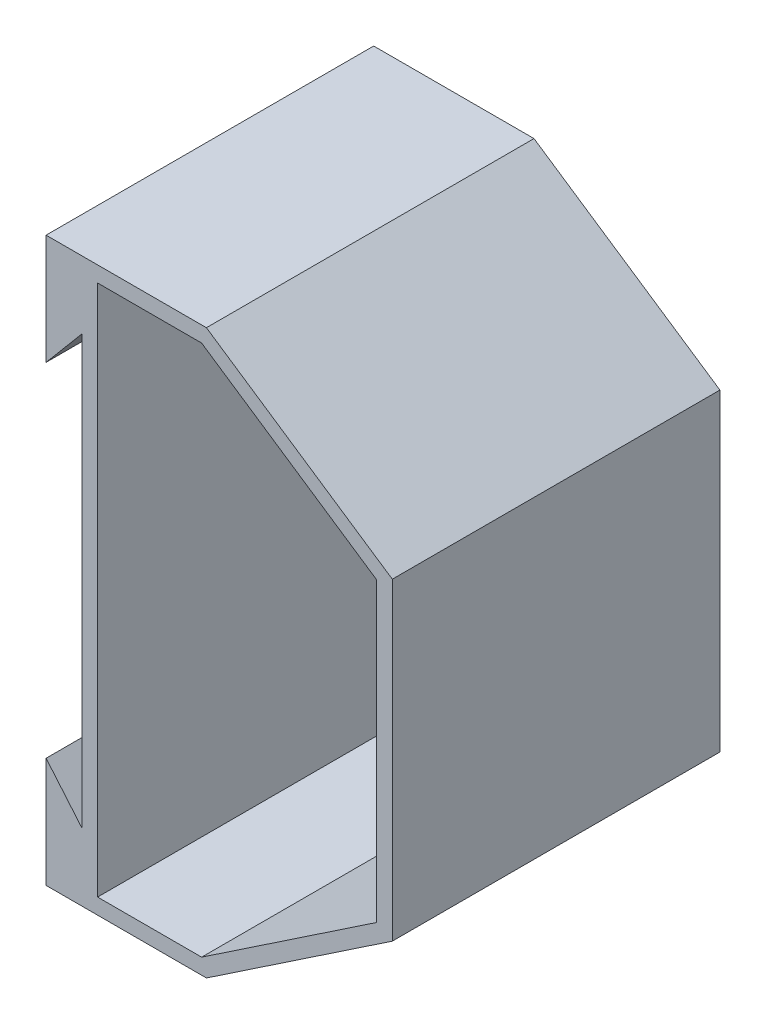
SolidWorks part; units mm, degrees
ref_plane "Alzado" through (0, 0, 0) normal (0, 0, 1) x (1, 0, 0)
ref_plane "Planta" through (0, 0, 0) normal (0, 1, 0) x (1, 0, 0)
ref_plane "Vista lateral" through (0, 0, 0) normal (1, 0, 0) x (0, 0, -1)
sketch "Croquis1" plane through (0, 0, 0) normal (0, 0, 1) x (1, 0, 0)
  line L0 (0, 0) -> (154.6177, 0) construction
  line L4 (154.6177, 70) -> (71.6, 125.75)
  line L5 (71.6, 125.75) -> (0, 125.75)
  line L6 (0, 125.75) -> (0, 76.55)
  line L7 (0, 76.55) -> (16, 95.55)
  line L8 (16, 95.55) -> (16, -95.55)
  line L11 (154.6177, -70) -> (71.6, -125.75)
  line L12 (71.6, -125.75) -> (0, -125.75)
  line L13 (0, -125.75) -> (0, -76.55)
  line L14 (0, -76.55) -> (16, -95.55)
  line L15 (154.6177, 70) -> (154.6177, -70)
  line L16 (147.6177, 66.2689) -> (69.4677, 118.75)
  line L17 (69.4677, 118.75) -> (23, 118.75)
  line L20 (23, 118.75) -> (23, -118.75)
  line L23 (69.4677, -118.75) -> (23, -118.75)
  line L24 (147.6177, -66.2689) -> (69.4677, -118.75)
  line L25 (147.6177, 66.2689) -> (147.6177, -66.2689)
  point P3 (0, 0)
  point P4 (154.6177, 0)
  point P5 (158.3678, 76.55)
  point P14 (0, 0)
  point P20 (16, 0)
  point P21 (81.0755, -113.0022)
  point P23 (145.9024, -71.3118)
  point P27 (0, 0)
  dimension "D1" = 100
  dimension "D2" = 71.6
  dimension "D3" = 49.2
  dimension "D4" = 153.1
  dimension "D5" = 19
  dimension "D6" = 16
  dimension "D7" = 140
  dimension "D8" = 7
  dimension "D9" = 7
  dimension "D10" = 7
  dimension "D11" = 7
  dimension "D12" = 7
  dimension "D13" = 7
extrude "Saliente-Extruir1" add sketch "Croquis1" along normal mid plane 146.3
